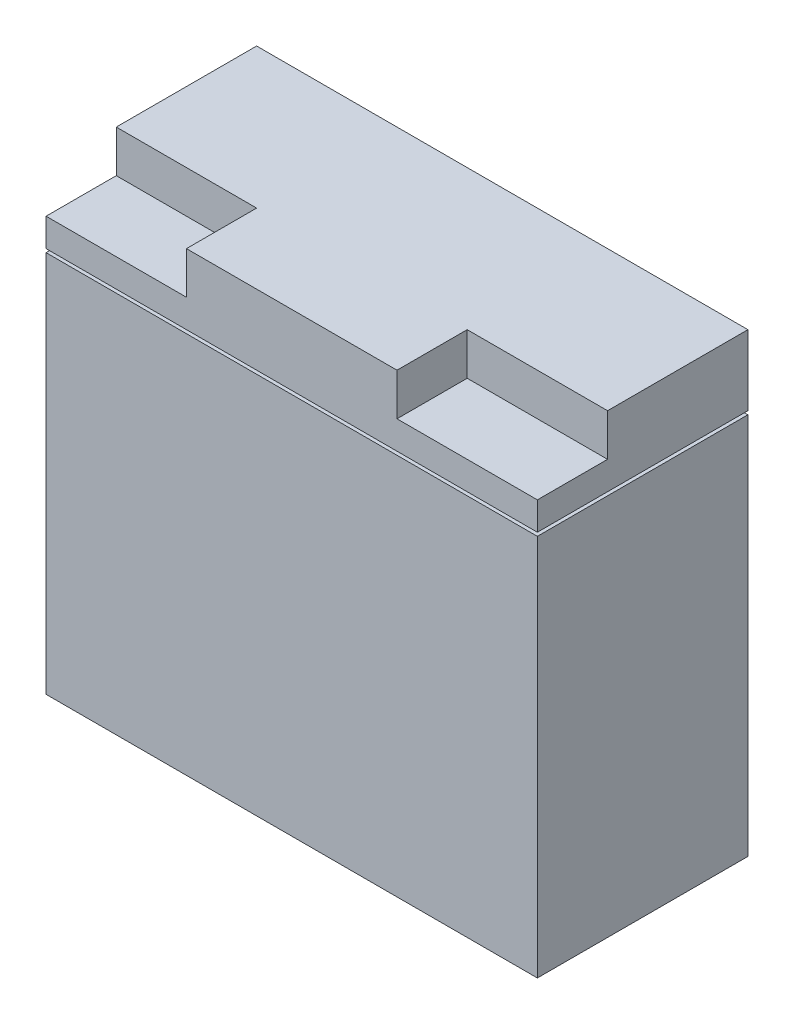
SolidWorks part; units mm, degrees
ref_plane "Front Plane" through (0, 0, 0) normal (0, 0, 1) x (1, 0, 0)
ref_plane "Top Plane" through (0, 0, 0) normal (0, 1, 0) x (1, 0, 0)
ref_plane "Right Plane" through (0, 0, 0) normal (1, 0, 0) x (0, 0, -1)
sketch "Sketch1" plane through (0, 0, 0) normal (0, 1, 0) x (1, 0, 0)
  line L1 (0, 0) -> (177.8, 0)
  line L2 (0, 0) -> (0, 76.2)
  line L3 (0, 76.2) -> (177.8, 76.2)
  line L4 (177.8, 0) -> (177.8, 76.2)
  line L5 (0, 0) -> (177.8, 76.2) construction
  line L6 (0, 76.2) -> (177.8, 0) construction
  point P4 (88.9, 38.1)
  dimension "D1" = 76.2
  dimension "D2" = 177.8
extrude "Boss-Extrude1" add sketch "Sketch1" along normal blind 165.1
sketch "Sketch2" plane through (0, 165.1, 0) normal (0, 1, 0) x (1, 0, 0)
  line L0 (88.9, 76.2) -> (88.9, 0) construction
  line L1 (0, 0) -> (50.8, 0)
  line L2 (0, 0) -> (0, 25.4)
  line L3 (0, 25.4) -> (50.8, 25.4)
  line L4 (50.8, 0) -> (50.8, 25.4)
  line L5 (0, 0) -> (50.8, 25.4) construction
  line L6 (0, 25.4) -> (50.8, 0) construction
  line L7 (177.8, 76.2) -> (0, 76.2) construction
  line L8 (0, 0) -> (177.8, 0) construction
  line L9 (177.8, 0) -> (177.8, 25.4)
  line L10 (177.8, 0) -> (127, 0)
  line L11 (127, 0) -> (127, 25.4)
  line L12 (177.8, 25.4) -> (127, 25.4)
  point P4 (25.4, 12.7)
  dimension "D1" = 25.4
  dimension "D2" = 50.8
extrude "Cut-Extrude1" cut sketch "Sketch2" against normal blind 15.24
ref_plane "Plane1" through (0, 139.7, 0) normal (0, 1, 0) x (1, 0, 0)
sketch "Sketch3" plane through (0, 139.7, 0) normal (0, 1, 0) x (1, 0, 0)
  line L0 (1.27, 74.93) -> (1.27, 1.27)
  line L1 (1.27, 1.27) -> (176.53, 1.27)
  line L2 (176.53, 1.27) -> (176.53, 74.93)
  line L3 (176.53, 74.93) -> (1.27, 74.93)
  line L4 (0, 76.2) -> (0, 0)
  line L5 (177.8, 76.2) -> (0, 76.2)
  line L6 (177.8, 0) -> (177.8, 76.2)
  line L7 (0, 0) -> (177.8, 0)
  line L8 (0, 76.2) -> (0, 0)
  line L9 (177.8, 76.2) -> (0, 76.2)
  line L10 (177.8, 0) -> (177.8, 76.2)
  line L11 (0, 0) -> (177.8, 0)
  dimension "D1" = 0
  dimension "D2" = 1.27
extrude "Cut-Extrude2" cut sketch "Sketch3" against normal blind 1.27
